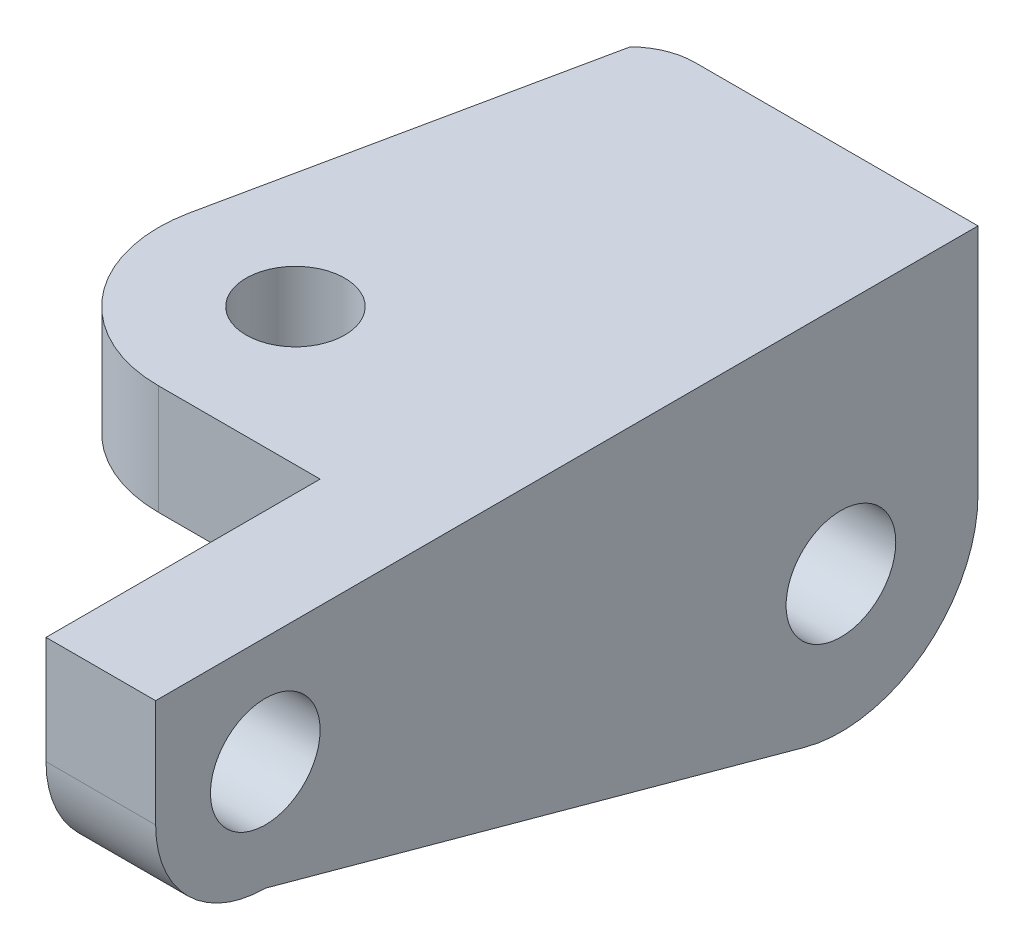
SolidWorks part; units mm, degrees
ref_plane "Front Plane" through (0, 0, 0) normal (0, 0, 1) x (1, 0, 0)
ref_plane "Top Plane" through (0, 0, 0) normal (0, 1, 0) x (1, 0, 0)
ref_plane "Right Plane" through (0, 0, 0) normal (1, 0, 0) x (0, 0, -1)
sketch "Sketch1" plane through (0, 0, 0) normal (1, 0, 0) x (0, 0, -1)
  line L0 (0, 0) -> (0, -19.63)
  line L1 (20, -39.63) -> (118.3977, -66.5724)
  line L2 (150, -42.46) -> (150, 0)
  line L3 (150, 0) -> (0, 0)
  arc A0 (0, -19.63) -> (20, -39.63) centre (20, -19.63) ccw
  arc A1 (118.3977, -66.5724) -> (150, -42.46) centre (125, -42.46) ccw
  circle A2 centre (20, -19.63) radius 10
  circle A3 centre (125, -42.46) radius 10
  dimension "D1" = 20
  dimension "D3" = 25
  dimension "D6" = 20
  dimension "D7" = 20
  dimension "D2" = 19.63
  dimension "D4" = 42.46
  dimension "D5" = 150
  dimension "D8" = 25
extrude "Boss-Extrude1" add sketch "Sketch1" along normal blind 20
sketch "Sketch2" plane through (0, 0, 0) normal (0, 1, 0) x (1, 0, 0)
  line L0 (0, 150) -> (-31.5939, 150)
  line L1 (-40, 146.5637) -> (-53.9651, 80.1439)
  line L2 (-29.5, 50) -> (0, 50)
  line L3 (0, 150) -> (0, 0) construction
  line L4 (0, 50) -> (0, 150)
  line L5 (20, 150) -> (20, 0) construction
  arc A0 (-31.5939, 150) -> (-40, 146.5637) centre (-31.5939, 138) ccw
  arc A1 (-53.9651, 80.1439) -> (-29.5, 50) centre (-29.5, 75) ccw
  circle A2 centre (-29.5, 75) radius 9
  point P13 (-15.797, 150)
  dimension "D1" = 25
  dimension "D3" = 12
  dimension "D6" = 18
  dimension "D2" = 49.5
  dimension "D4" = 100
  dimension "D5" = 75
  dimension "D7" = 60
extrude "Boss-Extrude2" add sketch "Sketch2" against normal blind 20
